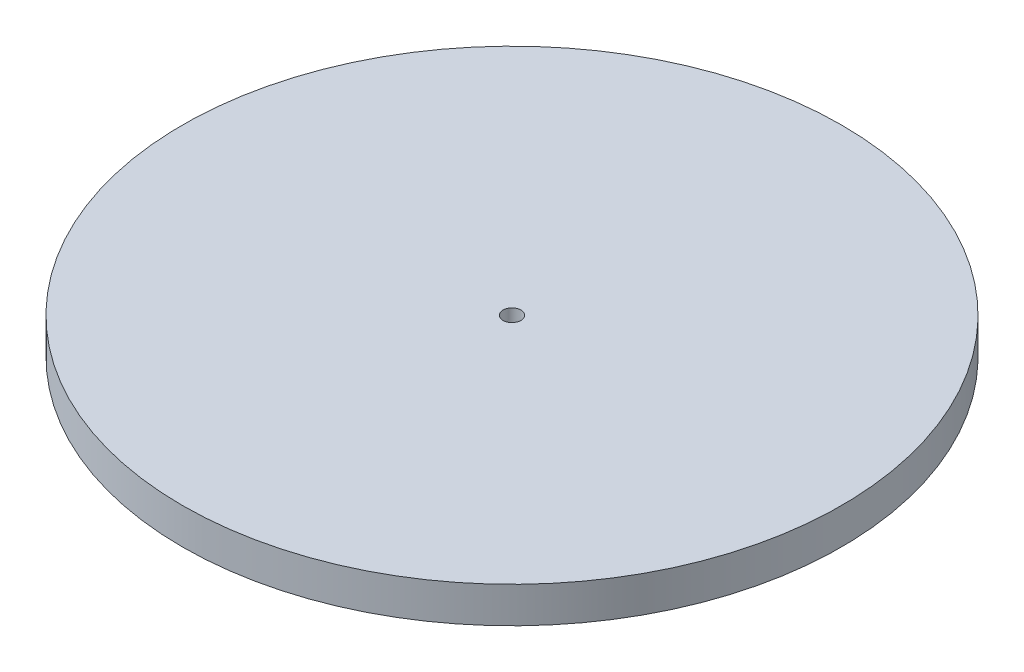
SolidWorks part; units mm, degrees
ref_plane "Front Plane" through (0, 0, 0) normal (0, 0, 1) x (1, 0, 0)
ref_plane "Top Plane" through (0, 0, 0) normal (0, 1, 0) x (1, 0, 0)
ref_plane "Right Plane" through (0, 0, 0) normal (1, 0, 0) x (0, 0, -1)
sketch "Sketch1" plane through (0, 0, 0) normal (0, 1, 0) x (1, 0, 0)
  circle A0 centre (0, 0) radius 27.5
  circle A1 centre (0, 0) radius 0.75
  dimension "D1" = 55
  dimension "D2" = 1.5
extrude "Boss-Extrude1" add sketch "Sketch1" along normal blind 3
